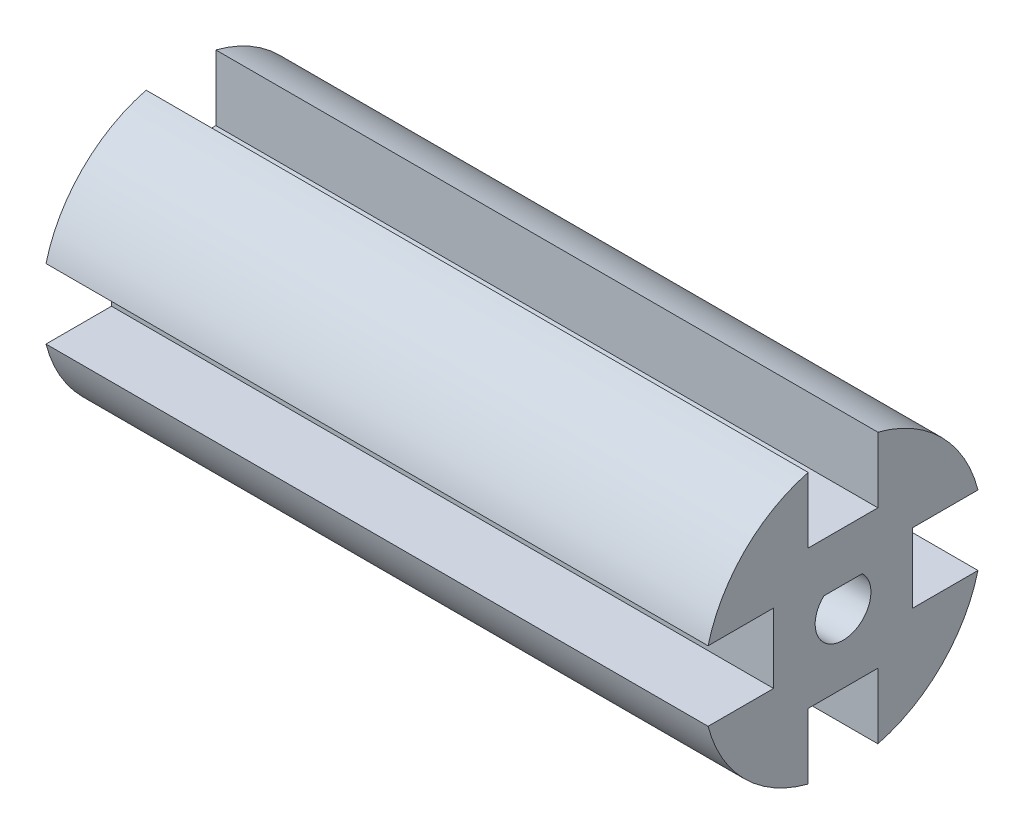
SolidWorks part; units mm, degrees
ref_plane "Front Plane" through (0, 0, 0) normal (0, 0, 1) x (1, 0, 0)
ref_plane "Top Plane" through (0, 0, 0) normal (0, 1, 0) x (1, 0, 0)
ref_plane "Right Plane" through (0, 0, 0) normal (1, 0, 0) x (0, 0, -1)
sketch "Sketch1" plane through (0, 0, 0) normal (1, 0, 0) x (0, 0, -1)
  line L1 (-5, -19.3649) -> (-5, -9.9649)
  line L2 (5, -19.3649) -> (5, -9.9649)
  line L4 (-19.3649, 5) -> (-9.9649, 5)
  line L5 (-19.3649, -5) -> (-9.9649, -5)
  line L7 (-5, 9.9649) -> (5, 9.9649)
  line L8 (9.9649, 5) -> (9.9649, -5)
  line L9 (-5, -9.9649) -> (5, -9.9649)
  line L10 (-9.9649, 5) -> (-9.9649, -5)
  line L11 (-5, 9.9649) -> (-5, 19.3649)
  line L13 (5, 9.9649) -> (5, 19.3649)
  line L16 (9.9649, -5) -> (19.3649, -5)
  line L18 (9.9649, 5) -> (19.3649, 5)
  circle A0 centre (0, 0) radius 20
  dimension "D1" = 40
  dimension "D2" = 10
  dimension "D3" = 10
  dimension "D4" = 10
  dimension "D5" = 9.4
  dimension "D6" = 9.4
  dimension "D7" = 9.4
  dimension "D8" = 9.4
  dimension "D9" = 9.4
extrude "Extruded Connector" add sketch "Sketch1" along normal blind 95 contours L18 A0 L13 L7 L11 L4 L10 L5 L1 L9 L2 L16 L8
sketch "Sketch2" plane through (95, 0, 0) normal (1, 0, 0) x (0, 0, -1)
  line L0 (-2.755, 2.9) -> (2.755, 2.9)
  circle A0 centre (0, 0) radius 4
  dimension "D1" = 8
  dimension "D2" = 2.9
extrude "Key Cut" cut sketch "Sketch2" against normal blind 20 contours L0 A0
